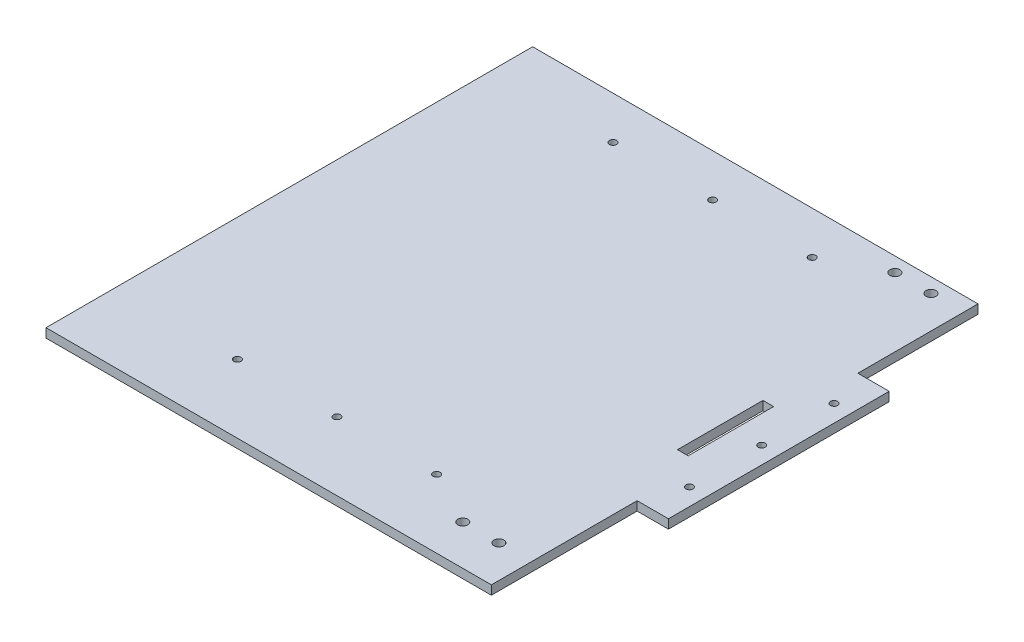
SolidWorks part; units mm, degrees
material "Cedar"
ref_plane "Front Plane" through (0, 0, 0) normal (0, 0, 1) x (1, 0, 0)
ref_plane "Top Plane" through (0, 0, 0) normal (0, 1, 0) x (1, 0, 0)
ref_plane "Right Plane" through (0, 0, 0) normal (1, 0, 0) x (0, 0, -1)
sketch "Sketch1" plane through (0, 0, 0) normal (0, 1, 0) x (1, 0, 0)
  line L0 (72.8376, -16.2766) -> (72.8376, -52.4668) construction
  line L1 (-156.5, -171) -> (156.5, -171)
  line L2 (-156.5, -171) -> (-156.5, 171)
  line L3 (-156.5, 171) -> (156.5, 171)
  line L4 (156.5, -171) -> (156.5, 171)
  line L5 (-156.5, -171) -> (156.5, 171) construction
  line L6 (-156.5, 171) -> (156.5, -171) construction
  point P0 (0, 0)
  dimension "D1" = 342
  dimension "D2" = 313
extrude "Boss-Extrude1" add sketch "Sketch1" against normal blind 6.35
ref_plane "Plane1" through (0, 0, -9) normal (0, 0, -1) x (-1, 0, 0)
sketch "Sketch3" plane through (0, 0, 0) normal (0, 1, 0) x (1, 0, 0)
  line L0 (156.5, 9) -> (-156.5, 9) construction
  line L1 (156.5, -171) -> (156.5, 171) construction
  line L2 (-156.5, 171) -> (-156.5, -171) construction
  line L3 (55, 9) -> (-55, 9) construction
  line L4 (156.5, 86.5702) -> (156.5, -68.5702)
  line L5 (156.5, -68.5702) -> (178.5, -68.5702)
  line L6 (178.5, -68.5702) -> (178.5, 86.5702)
  line L7 (178.5, 86.5702) -> (156.5, 86.5702)
  circle A0 centre (166.5, 9) radius 2.5
  circle A1 centre (166.5, -41.8) radius 2.5
  circle A2 centre (166.5, 59.8) radius 2.5
  point P10 (156.5, 9)
  dimension "D2" = 5
  dimension "D4" = 5
  dimension "D5" = 50.8
  dimension "D1" = 22
  dimension "D3" = 10
extrude "Boss-Extrude2" add sketch "Sketch3" against normal blind 6.35
sketch "Sketch2" plane through (0, 0, 0) normal (0, 1, 0) x (1, 0, 0)
  line L0 (156.5, 9) -> (-156.5, 9) construction
  line L1 (156.5, -171) -> (156.5, -68.5702) construction
  line L2 (-156.5, 171) -> (-156.5, -171) construction
  line L3 (0, -123) -> (0, -171) construction
  line L4 (55, 9) -> (-55, 9) construction
  line L5 (156.5, -123) -> (-156.5, -123) construction
  line L6 (-156.5, -171) -> (156.5, -171) construction
  circle A0 centre (0, -123) radius 2.5
  circle A1 centre (-70, -123) radius 2.5
  circle A2 centre (70, -123) radius 2.5
  circle A3 centre (-70, 141) radius 2.5
  circle A4 centre (0, 141) radius 2.5
  circle A5 centre (70, 141) radius 2.5
  dimension "D2" = 5
  dimension "D3" = 5
  dimension "D4" = 70
  dimension "D1" = 132
extrude "Cut-Extrude1" cut sketch "Sketch2" against normal through all
sketch "Sketch4" plane through (0, 0, 0) normal (0, 1, 0) x (1, 0, 0)
  line L0 (156.5, 171) -> (-156.5, 171) construction
  line L1 (156.5, 86.5702) -> (156.5, 171) construction
  circle A0 centre (133.64, 160.84) radius 3.5
  circle A1 centre (108.24, 160.84) radius 3.5
  point P6 (123.9534, 153.4308)
  dimension "D2" = 7
  dimension "D3" = 7
  dimension "D1" = 10.16
  dimension "D4" = 22.86
  dimension "D5" = 25.4
  dimension "D6" = 0
extrude "Cut-Extrude2" cut sketch "Sketch4" against normal through all
mirror "Mirror1" about plane through (0, 0, -9) normal (0, 0, -1) of "Cut-Extrude2"
sketch "Sketch5" plane through (0, 0, 0) normal (0, 1, 0) x (1, 0, 0)
  line L0 (139.6718, 36.6738) -> (147.1718, 36.6738)
  line L1 (147.1718, 36.6738) -> (147.1435, -23.3262)
  line L2 (147.1435, -23.3262) -> (139.6435, -23.3262)
  line L3 (139.6435, -23.3262) -> (139.6718, 36.6738)
extrude "Cut-Extrude3" cut sketch "Sketch5" against normal through all
